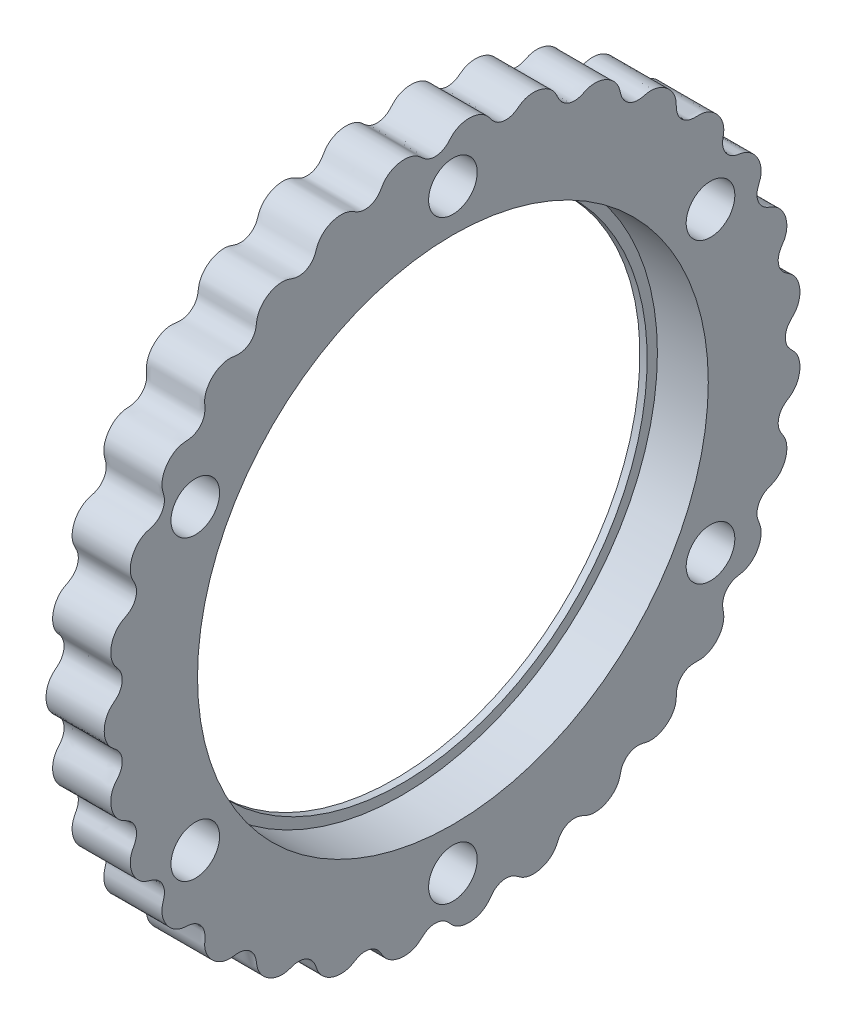
SolidWorks part; units mm, degrees
ref_plane "Front Plane" through (0, 0, 0) normal (0, 0, 1) x (1, 0, 0)
ref_plane "Top Plane" through (0, 0, 0) normal (0, 1, 0) x (1, 0, 0)
ref_plane "Right Plane" through (0, 0, 0) normal (1, 0, 0) x (0, 0, -1)
sketch "Sketch2" plane through (0, 0, 0) normal (0, 0, 1) x (1, 0, 0)
  line L0 (0, 0) -> (58.591, 0) construction
  line L2 (0, 0) -> (18.4, 0)
  line L3 (0, 0) -> (0, 2.5)
  line L4 (0, 2.5) -> (18.4, 2.5)
  line L5 (18.4, 0) -> (18.4, 2.5)
  line L6 (6.0094, 2.5) -> (6.0094, 6)
  line L11 (6.0094, 6) -> (9.9794, 6)
  line L16 (12.9794, 6) -> (12.9794, 3)
  line L17 (12.9794, 3) -> (13.6398, 3)
  line L18 (13.6398, 3) -> (13.6398, 2.5)
  line L19 (13.6398, 2.5) -> (6.0094, 2.5)
  line L22 (13.6398, 2.5) -> (16.1198, 2.5)
  line L23 (13.6398, 2.5) -> (13.6398, 4)
  line L24 (13.6398, 4) -> (16.1198, 4)
  line L25 (16.1198, 2.5) -> (16.1198, 4)
  line L27 (6.0094, 6) -> (9.9794, 6)
  line L28 (6.0094, 6) -> (6.0094, 9)
  line L29 (6.0094, 9) -> (9.9794, 9)
  line L30 (9.9794, 6) -> (9.9794, 9)
  line L31 (6.0094, 9) -> (6.0094, 8.25)
  line L32 (6.0094, 8.25) -> (5.0094, 8.25)
  line L33 (8.6609, 22.001) -> (8.6609, 12.476) construction
  line L34 (5.0094, 12.476) -> (12.3124, 12.476)
  line L35 (9.9794, 9) -> (12.3124, 9)
  line L36 (5.0094, 7.9375) -> (1.7709, 7.9375)
  line L37 (5.0094, 8.25) -> (5.0094, 12.476)
  line L38 (5.0094, 7.9375) -> (5.0094, 13.9365)
  line L39 (5.0094, 13.9365) -> (1.7709, 13.9365)
  line L40 (1.7709, 7.9375) -> (1.7709, 13.9365)
  line L41 (5.0094, 22.001) -> (12.3124, 22.001)
  line L42 (5.0094, 22.001) -> (5.0094, 30.1625)
  line L43 (5.0094, 30.1625) -> (12.3124, 30.1625)
  line L44 (12.3124, 22.001) -> (12.3124, 30.1625)
  line L49 (16.6398, 22.001) -> (16.6398, 7.5)
  line L51 (23.0198, 7.5) -> (23.0198, 6.5)
  line L54 (16.1198, 4) -> (13.6398, 4)
  line L56 (18.0398, 7.5) -> (23.0198, 7.5)
  line L57 (13.3124, 22.001) -> (16.6398, 22.001)
  line L58 (16.1198, 3.5) -> (20.0198, 3.5)
  line L59 (29.9098, 14) -> (26.9098, 11)
  line L60 (4.0094, 31.75) -> (18.0398, 31.75)
  line L61 (18.0398, 7.5) -> (23.0198, 7.5)
  line L62 (18.0398, 7.5) -> (18.0398, 12)
  line L63 (18.0398, 12) -> (23.0198, 12)
  line L64 (23.0198, 7.5) -> (23.0198, 12)
  line L65 (18.0398, 31.75) -> (18.0398, 12)
  line L66 (23.0198, 11) -> (26.9098, 11)
  line L67 (34.8098, 23) -> (31.3098, 19.5)
  line L68 (35.8098, 31) -> (38.7998, 33.99)
  line L69 (29.9098, 14) -> (29.9098, 15)
  line L70 (29.9098, 15) -> (22.9398, 15)
  line L71 (22.9398, 15) -> (21.0398, 15)
  line L72 (18.0398, 7.5) -> (16.6398, 7.5)
  line L73 (21.0398, 15) -> (21.0398, 43)
  line L74 (19.6115, 40) -> (9.6516, 40)
  line L75 (9.6516, 40) -> (4.0094, 40)
  line L76 (21.0398, 43) -> (19.6115, 43)
  line L77 (22.9398, 15) -> (29.9098, 15)
  line L78 (22.9398, 15) -> (22.9398, 21)
  line L79 (22.9398, 21) -> (29.9098, 21)
  line L80 (29.9098, 15) -> (29.9098, 21)
  line L81 (9.6516, 40) -> (19.6115, 40)
  line L82 (9.6516, 40) -> (9.6516, 50)
  line L83 (9.6516, 50) -> (19.6115, 50)
  line L84 (19.6115, 40) -> (19.6115, 50)
  line L85 (4.0094, 40) -> (4.0094, 31.75)
  line L86 (12.9794, 3) -> (12.9794, 2.5)
  line L87 (31.3098, 19.5) -> (29.9098, 19.5)
  line L88 (21.4694, 63.5) -> (21.4694, 51.308)
  line L89 (21.4694, 63.5) -> (25.9398, 63.5)
  line L90 (25.9398, 63.5) -> (25.9398, 25)
  line L91 (27.8398, 25) -> (25.9398, 25)
  line L92 (9.6516, 48) -> (8.2233, 48)
  line L93 (8.2233, 48) -> (8.2233, 53.476)
  line L94 (8.2233, 53.476) -> (19.6115, 53.476)
  line L95 (19.6115, 53.476) -> (19.6115, 50)
  line L96 (13.9174, 63.001) -> (13.9174, 53.476) construction
  line L97 (8.2233, 63.001) -> (19.6115, 63.001)
  line L98 (8.2233, 63.001) -> (8.2233, 68.2625)
  line L99 (8.2233, 68.2625) -> (19.6115, 68.2625)
  line L100 (19.6115, 63.001) -> (19.6115, 68.2625)
  line L101 (12.9794, 6) -> (11.9794, 6)
  line L102 (8.2233, 44.825) -> (4.9848, 44.825)
  line L103 (8.2233, 44.825) -> (8.2233, 54.9365)
  line L104 (8.2233, 54.9365) -> (4.9848, 54.9365)
  line L106 (9.9794, 6) -> (10.8794, 6)
  line L107 (27.8398, 25) -> (34.8098, 25)
  line L108 (34.8098, 25) -> (34.8098, 23)
  line L109 (0, 0) -> (-2, 0)
  line L110 (0, 0) -> (0, 11)
  line L111 (27.8398, 25) -> (34.8098, 25)
  line L112 (27.8398, 25) -> (27.8398, 32.5)
  line L113 (27.8398, 32.5) -> (34.8098, 32.5)
  line L114 (34.8098, 25) -> (34.8098, 32.5)
  line L115 (35.8098, 31) -> (34.8098, 31)
  line L116 (27.8398, 32.5) -> (27.8398, 64.5)
  line L117 (20.5849, 74.025) -> (6.2499, 74.025)
  line L118 (6.2499, 74.025) -> (6.2499, 76.2)
  line L119 (38.7998, 47.29) -> (30.8398, 55.25)
  line L120 (0, 11) -> (-2, 11)
  line L121 (38.7998, 43.815) -> (30.8623, 43.815)
  line L123 (-4.8152, 69.85) -> (1.5348, 76.2)
  line L124 (38.7998, 47.29) -> (38.7998, 33.99)
  line L125 (-2, 0) -> (-2, 11)
  line L126 (38.7998, 37.465) -> (30.8623, 37.465)
  line L127 (30.8623, 43.815) -> (30.8623, 37.465)
  line L128 (6.0094, 2.5) -> (6.0094, 0)
  line L129 (-0.0152, 63.5) -> (-0.0152, 30)
  line L132 (4.9848, 63.5) -> (-0.0152, 63.5)
  line L136 (-1.8152, 30) -> (-11.7752, 30)
  line L138 (-13.7752, 25.4) -> (-2, 25.4)
  line L139 (-2, 25.4) -> (-2, 11.5)
  line L140 (27.8398, 64.5) -> (20.5849, 64.5)
  line L141 (-1.8152, 30) -> (-11.7752, 30)
  line L142 (-1.8152, 30) -> (-1.8152, 39)
  line L143 (-1.8152, 39) -> (-11.7752, 39)
  line L144 (-11.7752, 30) -> (-11.7752, 39)
  line L145 (20.5849, 64.5) -> (20.5849, 74.025)
  line L146 (-12.7752, 37) -> (-12.7752, 47.29)
  line L147 (-12.7752, 37) -> (-11.7752, 37)
  line L148 (30.8398, 55.25) -> (30.8398, 76.2)
  line L149 (11.9794, 6) -> (11.9794, 5.45)
  line L154 (-2, 11.5) -> (0.5, 11.5)
  line L155 (4.9848, 60.6197) -> (24.0348, 60.6197)
  line L160 (4.9848, 60.6197) -> (4.9848, 55.8572)
  line L161 (4.9848, 55.8572) -> (24.0348, 55.8572)
  line L166 (24.0348, 60.6197) -> (24.0348, 55.8572)
  line L167 (4.9848, 60.6197) -> (24.0348, 55.8572) construction
  line L172 (4.9848, 55.8572) -> (24.0348, 60.6197) construction
  line L173 (24.0348, 62.2072) -> (25.9398, 62.2072)
  line L174 (11.9794, 5.45) -> (10.8794, 5.45)
  line L175 (10.8794, 6) -> (10.8794, 5.45)
  line L176 (24.0348, 62.2072) -> (24.0348, 54.2697)
  line L177 (24.0348, 54.2697) -> (25.9398, 54.2697)
  line L178 (25.9398, 62.2072) -> (25.9398, 54.2697)
  line L179 (24.0348, 62.2072) -> (25.9398, 54.2697) construction
  line L180 (24.0348, 54.2697) -> (25.9398, 62.2072) construction
  line L181 (3, 19.6197) -> (15.7, 19.6197)
  line L182 (3, 19.6197) -> (3, 14.8572)
  line L183 (3, 14.8572) -> (15.7, 14.8572)
  line L184 (15.7, 19.6197) -> (15.7, 14.8572)
  line L185 (3, 19.6197) -> (15.7, 14.8572) construction
  line L186 (3, 14.8572) -> (15.7, 19.6197) construction
  line L187 (15.7, 21.2072) -> (16.6398, 21.2072)
  line L188 (15.7, 21.2072) -> (15.7, 13.2697)
  line L189 (15.7, 13.2697) -> (16.6398, 13.2697)
  line L190 (16.6398, 21.2072) -> (16.6398, 13.2697)
  line L191 (15.7, 21.2072) -> (16.6398, 13.2697) construction
  line L192 (15.7, 13.2697) -> (16.6398, 21.2072) construction
  line L193 (0.5, 11.5) -> (0.5, 6.9375)
  line L194 (0.5, 6.9375) -> (1.7709, 6.9375)
  line L195 (23.0198, 6.5) -> (20.0198, 3.5)
  line L196 (4.9848, 63.5) -> (4.9848, 54.9365)
  line L197 (3, 43.825) -> (4.9848, 43.825)
  line L198 (1.7709, 6.9375) -> (1.7709, 7.9375)
  line L199 (6.0094, 0) -> (12.9794, 0)
  line L200 (12.9794, 0) -> (12.9794, 2.5)
  line L201 (18.0398, 31.75) -> (18.0398, 35.875)
  line L202 (18.0398, 35.875) -> (21.0398, 35.875)
  line L203 (30.8398, 76.2) -> (6.2499, 76.2)
  line L204 (2.8049, 69.85) -> (7.2499, 69.85) construction
  line L205 (7.2499, 67.4688) -> (26.2999, 67.4688)
  line L206 (7.2499, 74.025) -> (7.2499, 64.5)
  line L207 (7.2499, 64.5) -> (-1.8152, 64.5)
  line L208 (-1.8152, 64.5) -> (-1.8152, 39)
  line L209 (-12.7752, 47.29) -> (-4.8152, 55.25)
  line L210 (-4.8152, 55.25) -> (-4.8152, 69.85)
  line L211 (7.2499, 67.4688) -> (7.2499, 72.2312)
  line L212 (7.2499, 72.2312) -> (26.2999, 72.2313)
  line L213 (26.2999, 67.4688) -> (26.2999, 72.2313)
  line L214 (26.2999, 73.8187) -> (30.8398, 73.8187)
  line L215 (26.2999, 73.8187) -> (26.2999, 65.8813)
  line L216 (26.2999, 65.8813) -> (30.8398, 65.8813)
  line L217 (30.8398, 73.8187) -> (30.8398, 65.8813)
  line L218 (2.8049, 72.2313) -> (25.0299, 72.2313)
  line L219 (2.8049, 72.2313) -> (2.8049, 67.4687)
  line L220 (2.8049, 67.4687) -> (25.0299, 67.4687)
  line L221 (25.0299, 72.2313) -> (25.0299, 67.4687)
  line L222 (25.0299, 69.85) -> (20.5849, 69.85) construction
  line L223 (21.4694, 51.308) -> (22.9398, 51.308)
  line L224 (22.9398, 51.308) -> (22.9398, 21)
  line L225 (13.6398, 4) -> (13.6398, 12.2697)
  line L226 (13.6398, 12.2697) -> (13.3124, 12.2697)
  line L227 (13.3124, 12.2697) -> (13.3124, 22.001)
  line L228 (12.3124, 9) -> (12.3124, 12.476)
  line L229 (-1.8152, 30) -> (-0.0152, 30)
  line L230 (8.2233, 65.6317) -> (2.8049, 65.6317) construction
  line L231 (19.6115, 65.6317) -> (25.0299, 65.6317) construction
  line L232 (1.5348, 76.2) -> (6.2499, 76.2)
  line L233 (-11.7752, 30) -> (-13.7752, 30)
  line L234 (-13.7752, 30) -> (-13.7752, 25.4)
  line L235 (3, 13.9365) -> (3, 43.825)
  line L236 (4.9848, 54.9365) -> (4.9848, 44.825)
  line L237 (4.9848, 43.825) -> (4.9848, 44.825)
  circle A0 centre (26.8898, 25.95) radius 0.95
  circle A1 centre (21.9898, 15.95) radius 0.95
  circle A2 centre (17.3398, 8.2) radius 0.7
  circle A3 centre (10.4294, 6.45) radius 0.45
  circle A4 centre (-0.9152, 30.9) radius 0.9
  point P7 (24.9873, 58.2385)
  point P131 (16.1699, 17.2385)
  point P135 (14.5098, 58.2385)
  point P146 (9.35, 17.2385)
sketch "Sketch3" plane through (0, 0, 0) normal (1, 0, 0) x (0, 0, -1)
  line L0 (0, 0) -> (0, 69.85) construction
  line L1 (0, 0) -> (13.6271, 68.5079) construction
  line L2 (0, 0) -> (0, 58.2385) construction
  line L3 (0, 0) -> (50.436, 29.1192) construction
  line L4 (0, 0) -> (0, 31.75) construction
  line L5 (0, 0) -> (12.1502, 29.3332) construction
  line L6 (0, 0) -> (0, 17.2385) construction
  line L7 (0, 0) -> (14.929, 8.6192) construction
  line L8 (0, 0) -> (0, 58.2385) construction
  line L9 (0, 0) -> (50.436, 29.1192) construction
  line L10 (0, 0) -> (5.9583, 29.9542) construction
  line L11 (0, 0) -> (16.9677, 25.394) construction
  circle A0 centre (0, 0) radius 69.85 construction
  circle A1 centre (0, 0) radius 58.2385 construction
  circle A2 centre (0, 0) radius 31.75 construction
  circle A3 centre (0, 0) radius 17.2385 construction
  circle A4 centre (0, 69.85) radius 3.175
  circle A5 centre (0, 58.2385) radius 4.7625
  circle A6 centre (0, 31.75) radius 3.175
  circle A7 centre (0, 17.2385) radius 4.7625
  circle A8 centre (13.6271, 68.5079) radius 3.175
  circle A9 centre (26.7304, 64.533) radius 3.175
  circle A10 centre (38.8066, 58.0782) radius 3.175
  circle A11 centre (49.3914, 49.3914) radius 3.175
  circle A12 centre (58.0782, 38.8066) radius 3.175
  circle A13 centre (64.533, 26.7304) radius 3.175
  circle A14 centre (68.5079, 13.6271) radius 3.175
  circle A15 centre (69.85, 0) radius 3.175
  circle A16 centre (68.5079, -13.6271) radius 3.175
  circle A17 centre (64.533, -26.7304) radius 3.175
  circle A18 centre (58.0782, -38.8066) radius 3.175
  circle A19 centre (49.3914, -49.3914) radius 3.175
  circle A20 centre (38.8066, -58.0782) radius 3.175
  circle A21 centre (26.7304, -64.533) radius 3.175
  circle A22 centre (13.6271, -68.5079) radius 3.175
  circle A23 centre (0, -69.85) radius 3.175
  circle A24 centre (-13.6271, -68.5079) radius 3.175
  circle A25 centre (-26.7304, -64.533) radius 3.175
  circle A26 centre (-38.8066, -58.0782) radius 3.175
  circle A27 centre (-49.3914, -49.3914) radius 3.175
  circle A28 centre (-58.0782, -38.8066) radius 3.175
  circle A29 centre (-64.533, -26.7304) radius 3.175
  circle A30 centre (-68.5079, -13.6271) radius 3.175
  circle A31 centre (-69.85, 0) radius 3.175
  circle A32 centre (-68.5079, 13.6271) radius 3.175
  circle A33 centre (-64.533, 26.7304) radius 3.175
  circle A34 centre (-58.0782, 38.8066) radius 3.175
  circle A35 centre (-49.3914, 49.3914) radius 3.175
  circle A36 centre (-38.8066, 58.0782) radius 3.175
  circle A37 centre (-26.7304, 64.533) radius 3.175
  circle A38 centre (-13.6271, 68.5079) radius 3.175
  circle A47 centre (50.436, 29.1192) radius 4.7625
  circle A48 centre (50.436, -29.1192) radius 4.7625
  circle A49 centre (0, -58.2385) radius 4.7625
  circle A50 centre (-50.436, -29.1192) radius 4.7625
  circle A51 centre (-50.436, 29.1192) radius 4.7625
  circle A58 centre (12.1502, 29.3332) radius 3.175
  circle A59 centre (22.4506, 22.4506) radius 3.175
  circle A60 centre (29.3332, 12.1502) radius 3.175
  circle A61 centre (31.75, 0) radius 3.175
  circle A62 centre (29.3332, -12.1502) radius 3.175
  circle A63 centre (22.4506, -22.4506) radius 3.175
  circle A64 centre (12.1502, -29.3332) radius 3.175
  circle A65 centre (0, -31.75) radius 3.175
  circle A66 centre (-12.1502, -29.3332) radius 3.175
  circle A67 centre (-22.4506, -22.4506) radius 3.175
  circle A68 centre (-29.3332, -12.1502) radius 3.175
  circle A69 centre (-31.75, 0) radius 3.175
  circle A70 centre (-29.3332, 12.1502) radius 3.175
  circle A71 centre (-22.4506, 22.4506) radius 3.175
  circle A72 centre (14.929, 8.6192) radius 4.7625
  circle A73 centre (14.929, -8.6192) radius 4.7625
  circle A74 centre (0, -17.2385) radius 4.7625
  circle A75 centre (-14.929, -8.6192) radius 4.7625
  circle A76 centre (-14.929, 8.6192) radius 4.7625
  circle A77 centre (0, 0) radius 50
  circle A78 centre (0, 0) radius 9
  circle A79 centre (-12.1502, 29.3332) radius 3.175
  circle A80 centre (0, 0) radius 76.2
  circle A81 centre (0, 0) radius 74.025
  circle A82 centre (0, 69.85) radius 3.9687
  circle A83 centre (49.3914, 49.3914) radius 3.9687
  circle A84 centre (69.85, 0) radius 3.9688
  circle A85 centre (49.3914, -49.3914) radius 3.9687
  circle A86 centre (0, -69.85) radius 3.9687
  circle A87 centre (-49.3914, -49.3914) radius 3.9687
  circle A88 centre (-69.85, 0) radius 3.9688
  circle A89 centre (-49.3914, 49.3914) radius 3.9687
  circle A90 centre (0, 69.85) radius 2.3812
  circle A91 centre (13.6271, 68.5079) radius 2.3812
  circle A92 centre (26.7304, 64.533) radius 2.3813
  circle A93 centre (38.8066, 58.0782) radius 2.3812
  circle A94 centre (49.3914, 49.3914) radius 2.3812
  circle A95 centre (58.0782, 38.8066) radius 2.3812
  circle A96 centre (64.533, 26.7304) radius 2.3813
  circle A97 centre (68.5079, 13.6271) radius 2.3813
  circle A98 centre (69.85, 0) radius 2.3813
  circle A99 centre (68.5079, -13.6271) radius 2.3813
  circle A100 centre (64.533, -26.7304) radius 2.3813
  circle A101 centre (58.0782, -38.8066) radius 2.3812
  circle A102 centre (49.3914, -49.3914) radius 2.3812
  circle A103 centre (38.8066, -58.0782) radius 2.3812
  circle A104 centre (26.7304, -64.533) radius 2.3813
  circle A105 centre (13.6271, -68.5079) radius 2.3812
  circle A106 centre (0, -69.85) radius 2.3812
  circle A107 centre (-13.6271, -68.5079) radius 2.3812
  circle A108 centre (-26.7304, -64.533) radius 2.3813
  circle A109 centre (-38.8066, -58.0782) radius 2.3812
  circle A110 centre (-49.3914, -49.3914) radius 2.3812
  circle A111 centre (-58.0782, -38.8066) radius 2.3812
  circle A112 centre (-64.533, -26.7304) radius 2.3812
  arc A113 (3.0399, 30.8338) -> (8.9911, 29.65) centre (5.9583, 29.9542) cw
  arc A114 (14.6081, 27.3234) -> (19.6532, 23.9523) centre (16.9677, 25.394) cw
  arc A115 (23.9523, 19.6532) -> (27.3234, 14.6081) centre (25.394, 16.9677) cw
  arc A116 (29.65, 8.9911) -> (30.8338, 3.0399) centre (29.9542, 5.9583) cw
  arc A117 (30.8338, -3.0399) -> (29.65, -8.9911) centre (29.9542, -5.9583) cw
  arc A118 (27.3234, -14.6081) -> (23.9523, -19.6532) centre (25.394, -16.9677) cw
  arc A119 (19.6532, -23.9523) -> (14.6081, -27.3234) centre (16.9677, -25.394) cw
  arc A120 (8.9911, -29.65) -> (3.0399, -30.8338) centre (5.9583, -29.9542) cw
  arc A121 (-3.0399, -30.8338) -> (-8.9911, -29.65) centre (-5.9583, -29.9542) cw
  arc A122 (-14.6081, -27.3234) -> (-19.6532, -23.9523) centre (-16.9677, -25.394) cw
  arc A123 (-23.9523, -19.6532) -> (-27.3234, -14.6081) centre (-25.394, -16.9677) cw
  arc A124 (-29.65, -8.9911) -> (-30.8338, -3.0399) centre (-29.9542, -5.9583) cw
  arc A125 (-30.8338, 3.0399) -> (-29.65, 8.9911) centre (-29.9542, 5.9583) cw
  arc A126 (-27.3234, 14.6081) -> (-23.9523, 19.6532) centre (-25.394, 16.9677) cw
  arc A127 (-19.6532, 23.9523) -> (-14.6081, 27.3234) centre (-16.9677, 25.394) cw
  arc A128 (-8.9911, 29.65) -> (-3.0399, 30.8338) centre (-5.9583, 29.9542) cw
  arc A129 (26.9875, 0) -> (26.9932, 0.1932) centre (30.2705, 0) cw
  arc A130 (65.0988, 0.2771) -> (65.0875, 0) centre (68.4964, 0) ccw
  circle A131 centre (1.5875, 0) radius 40
  circle A132 centre (1.5875, 0) radius 2.5
  circle A133 centre (1.5875, 0) radius 3
  circle A134 centre (1.5875, 0) radius 43
  circle A135 centre (-68.5079, -13.6271) radius 2.3813
  circle A136 centre (-69.85, 0) radius 2.3813
  circle A137 centre (-68.5079, 13.6271) radius 2.3813
  circle A138 centre (-64.533, 26.7304) radius 2.3812
  circle A139 centre (-58.0782, 38.8066) radius 2.3812
  circle A140 centre (-49.3914, 49.3914) radius 2.3812
  circle A141 centre (-38.8066, 58.0782) radius 2.3812
  circle A142 centre (-26.7304, 64.533) radius 2.3813
  circle A143 centre (-13.6271, 68.5079) radius 2.3812
  circle A144 centre (0, 58.2385) radius 2.3812
  circle A145 centre (0, 58.2385) radius 3.9688
  circle A146 centre (50.436, 29.1192) radius 3.9688
  circle A147 centre (50.436, 29.1192) radius 2.3813
  circle A148 centre (50.436, -29.1192) radius 3.9687
  circle A149 centre (50.436, -29.1192) radius 2.3812
  circle A150 centre (0, -58.2385) radius 3.9687
  circle A151 centre (0, -58.2385) radius 2.3812
  circle A152 centre (-50.436, -29.1192) radius 3.9687
  circle A153 centre (-50.436, -29.1192) radius 2.3812
  circle A154 centre (-50.436, 29.1192) radius 3.9687
  circle A155 centre (-50.436, 29.1192) radius 2.3812
  spline S1 degree 4 number of poles 499 (26.9875, 0) -> (26.9932, 0.1932)
  spline S3 degree 4 number of poles 617 (65.0875, 0) -> (65.0988, 0.2771)
  point P116 (0, 0)
  point P225 (0, 0)
sketch "Sketch6" plane through (0, 0, 0) normal (0, 0, 1) x (1, 0, 0)
  line L0 (19.6115, 53.476) -> (19.6115, 50) construction
  line L1 (9.6516, 50) -> (19.6115, 50) construction
  line L2 (9.6516, 40) -> (9.6516, 50) construction
  line L3 (9.6516, 48) -> (8.2233, 48) construction
  line L4 (8.2233, 48) -> (8.2233, 53.476) construction
  line L5 (8.2233, 53.476) -> (19.6115, 53.476) construction
  line L6 (19.6115, 53.476) -> (19.6115, 50)
  line L7 (9.6516, 50) -> (19.6115, 50)
  line L8 (9.6516, 48) -> (9.6516, 50)
  line L9 (9.6516, 48) -> (8.2233, 48)
  line L10 (8.2233, 48) -> (8.2233, 53.476)
  line L11 (8.2233, 53.476) -> (19.6115, 53.476)
revolve "Revolve2" add sketch "Sketch6" angle 360 about L0
sketch "Sketch7" plane through (0, 0, 0) normal (1, 0, 0) x (0, 0, -1)
  circle A0 centre (0, 0) radius 50 construction
  circle A1 centre (-50.436, -29.1192) radius 4.7625 construction
  circle A2 centre (0, -58.2385) radius 4.7625 construction
  circle A3 centre (50.436, -29.1192) radius 4.7625 construction
  circle A4 centre (50.436, 29.1192) radius 4.7625 construction
  circle A5 centre (0, 58.2385) radius 4.7625 construction
  circle A6 centre (-50.436, 29.1192) radius 4.7625 construction
  circle A7 centre (0, 0) radius 50
  circle A8 centre (-50.436, -29.1192) radius 4.7625
  circle A9 centre (0, -58.2385) radius 4.7625
  circle A10 centre (50.436, -29.1192) radius 4.7625
  circle A11 centre (50.436, 29.1192) radius 4.7625
  circle A12 centre (0, 58.2385) radius 4.7625
  circle A13 centre (-50.436, 29.1192) radius 4.7625
  arc A14 (65.0988, 0.2771) -> (65.0875, 0) centre (68.4964, 0) ccw construction
  arc A15 (65.0988, 0.2771) -> (65.0875, 0) centre (68.4964, 0) ccw
  spline S0 degree 4 number of poles 617 (65.0875, 0) -> (65.0988, 0.2771) construction
  spline S1 degree 4 number of poles 617 (65.0875, 0) -> (65.0988, 0.2771)
extrude "Boss-Extrude1" add sketch "Sketch7" along normal up to vertex (19.6116 mm away) from vertex at 8.2233 starting at point (8.2233, 68.2625, 0)
